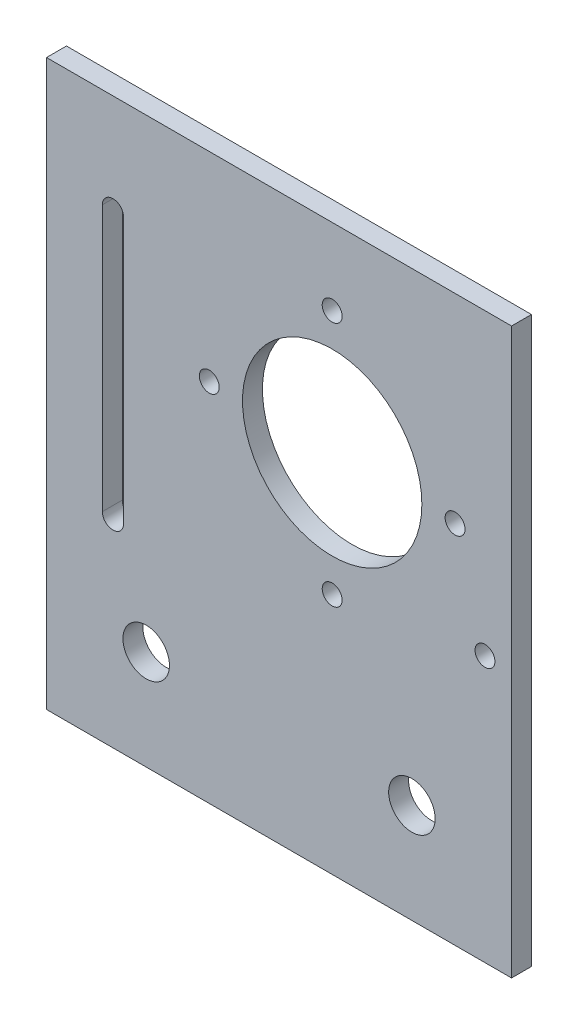
SolidWorks part; units mm, degrees
ref_plane "Front Plane" through (0, 0, 0) normal (0, 0, 1) x (1, 0, 0)
ref_plane "Top Plane" through (0, 0, 0) normal (0, 1, 0) x (1, 0, 0)
ref_plane "Right Plane" through (0, 0, 0) normal (1, 0, 0) x (0, 0, -1)
sketch "Sketch1" plane through (0, 0, 0) normal (0, 0, 1) x (1, 0, 0)
  line L1 (-35, 42.5) -> (35, 42.5)
  line L2 (-35, 42.5) -> (-35, -42.5)
  line L3 (-35, -42.5) -> (35, -42.5)
  line L4 (35, 42.5) -> (35, -42.5)
  line L5 (-35, 42.5) -> (35, -42.5) construction
  line L6 (-35, -42.5) -> (35, 42.5) construction
  line L8 (-26.6, 27.5) -> (-26.6, -12.5)
  line L10 (-23.4, 27.5) -> (-23.4, -12.5)
  circle A0 centre (31, -2.5) radius 1.5
  circle A1 centre (8, 12.5) radius 13.5
  arc A2 (-23.4, 27.5) -> (-26.6, 27.5) centre (-25, 27.5) ccw
  circle A3 centre (-20, -27.5) radius 3.5
  circle A4 centre (20, -27.5) radius 3.5
  circle A5 centre (8, 31) radius 1.5
  circle A6 centre (26.5, 12.5) radius 1.5
  circle A7 centre (8, -6) radius 1.5
  circle A8 centre (-10.5, 12.5) radius 1.5
  arc A9 (-26.6, -12.5) -> (-23.4, -12.5) centre (-25, -12.5) ccw
  point P0 (0, 0)
  point P15 (-24.7356, 7.5)
  point P32 (-23.2239, 26.988)
  dimension "D3" = 27
  dimension "D4" = 15
  dimension "D9" = 40
  dimension "D10" = 3
  dimension "D11" = 4
  dimension "D15" = 3
  dimension "D16" = 7
  dimension "D1" = 70
  dimension "D2" = 85
  dimension "D5" = 55
  dimension "D6" = 43
  dimension "D7" = 15
  dimension "D8" = 40
  dimension "D12" = 3.2
  dimension "D13" = 40
  dimension "D14" = 10
extrude "Boss-Extrude1" add sketch "Sketch1" along normal blind 3
